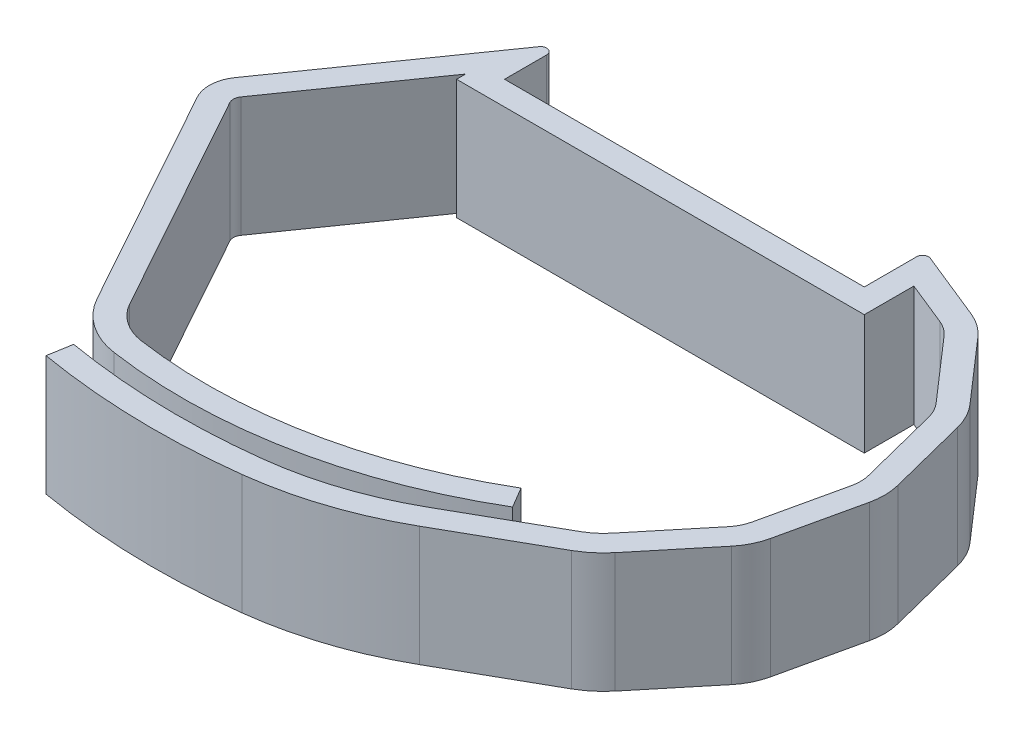
SolidWorks part; units mm, degrees
ref_plane "Front Plane" through (0, 0, 0) normal (0, 0, 1) x (1, 0, 0)
ref_plane "Top Plane" through (0, 0, 0) normal (0, 1, 0) x (1, 0, 0)
ref_plane "Right Plane" through (0, 0, 0) normal (1, 0, 0) x (0, 0, -1)
sketch "Sketch1" plane through (0, 0, 0) normal (0, 1, 0) x (1, 0, 0)
  line L25 (0, 0) -> (30, 0)
  line L26 (0, 0) -> (0, 5.1)
  line L27 (0, 5.1) -> (-11.3568, -11.1192)
  line L28 (-11.5142, -14.1151) -> (-1.1434, -32.8343)
  line L29 (30, 0) -> (30, 5.1)
  line L30 (30, 5.1) -> (36.396, 2.5112)
  line L31 (38.3662, 1.1076) -> (42.9025, -4.0916)
  line L32 (44.0261, -6.234) -> (45.7239, -12.9219)
  line L33 (45.7583, -15.3407) -> (44.2512, -22.0741)
  line L34 (43.189, -24.2476) -> (38.8023, -29.5737)
  line L35 (36.8101, -31.2464) -> (28.7168, -35.8276)
  line L36 (43.189, -24.2476) -> (44.2512, -22.0741) construction
  line L37 (45.7583, -15.3407) -> (45.7239, -12.9219) construction
  line L38 (44.0261, -6.234) -> (42.9025, -4.0916) construction
  line L39 (38.3662, 1.1076) -> (36.396, 2.5112) construction
  arc A0 (-11.3568, -11.1192) -> (-11.5142, -14.1151) centre (-9.0377, -12.7431) ccw
  arc A1 (-1.1434, -32.8343) -> (3.45, -36.0108) centre (4.3601, -29.7852) ccw
  arc A2 (36.396, 2.5112) -> (38.3662, 1.1076) centre (34.4421, -2.3162) cw
  arc A3 (42.9025, -4.0916) -> (44.0261, -6.234) centre (38.9783, -7.5154) cw
  arc A4 (45.7239, -12.9219) -> (45.7583, -15.3407) centre (40.6761, -14.2033) cw
  arc A5 (44.2512, -22.0741) -> (43.189, -24.2476) centre (39.1691, -20.9367) cw
  arc A6 (38.8023, -29.5737) -> (36.8101, -31.2464) centre (33.2962, -25.0387) cw
  arc A7 (28.7168, -35.8276) -> (17.6013, -39.4854) centre (14.0041, -9.8357) cw
  arc A8 (3.45, -36.0108) -> (31.228, -30.5569) centre (9.6063, 6.1007) ccw
  arc A9 (17.6013, -39.4854) -> (0.8423, -39.0787) centre (10.6143, 18.1035) cw
  dimension "D8" = 6.9
  dimension "D1" = 5.1
  dimension "D2" = 30
  dimension "D3" = 19.8
  dimension "D4" = 21.4
  dimension "D5" = 3
  dimension "D6" = 6.9
  dimension "D7" = 9.3
  dimension "D13" = 67.964
extrude "Extrude-Thin1" add sketch "Sketch1" along normal blind 10 thin contours A9 A7 L35 A6 L34 A5 L33 A4 L32 A3 L31 A2 L30 L29 L25 L26 L27 A0 L28 A1 A8
fillet "Fillet1" radius 0.5 2 edges at (0, 5, -5.1) (30, 5, -5.1)
